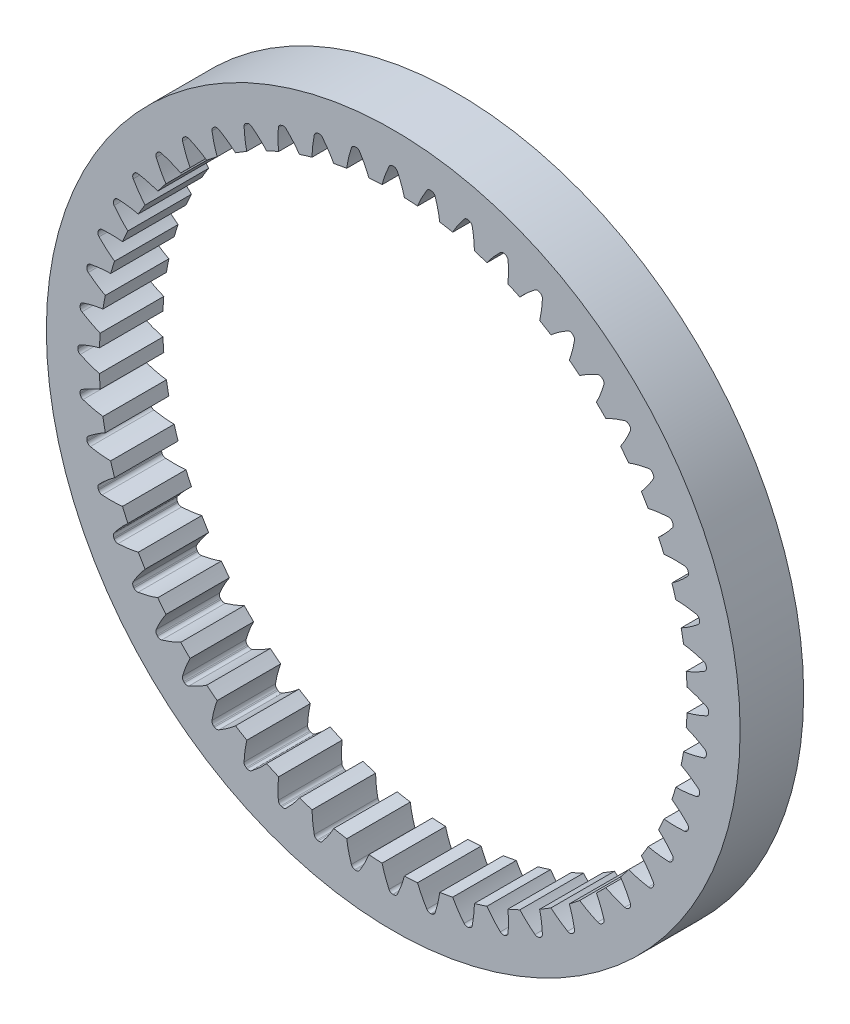
SolidWorks part; units mm, degrees
ref_plane "Front Plane" through (0, 0, 0) normal (0, 0, 1) x (1, 0, 0)
ref_plane "Top Plane" through (0, 0, 0) normal (0, 1, 0) x (1, 0, 0)
ref_plane "Right Plane" through (0, 0, 0) normal (1, 0, 0) x (0, 0, -1)
ref_axis "Axis1" through (0, 0, 2.8875) along (0, 0, -1)
sketch "Sketch3" plane through (0, 0, 0) normal (0, 0, 1) x (1, 0, 0)
  circle A0 centre (0, 0) radius 15.015
  circle A1 centre (0, 0) radius 12.725
  dimension "D1" = 30.03
  dimension "D2" = 25.45
extrude "Boss-Extrude2" add sketch "Sketch3" along normal blind 2.75
sketch "Sketch1" plane through (0, 0, 0) normal (0, 0, 1) x (1, 0, 0)
  line L8 (13.5488, 0.1808) -> (13.5488, -0.1808) construction
  line L10 (12.7158, 0.4827) -> (12.7158, -0.4827)
  line L11 (13.65, 0.0227) -> (13.65, -0.0227)
  circle A0 centre (0, 0) radius 12.725 construction
  circle A4 centre (0, 0) radius 13.65 construction
  arc A5 (13.5488, 0.1808) -> (13.65, 0.0227) centre (13.4753, 0.0224) cw
  arc A6 (13.5488, -0.1808) -> (13.65, -0.0227) centre (13.4753, -0.0224) ccw
  spline S0 degree 4 poles (12.6523, 0.498) (12.6569, 0.4969) (12.6657, 0.4949) (12.6776, 0.4921) (12.7085, 0.4845) (12.7233, 0.4808) (12.761, 0.4711) (12.7837, 0.465) (12.8146, 0.4565) (12.8404, 0.4491) (12.8693, 0.4407) (12.8962, 0.4326) (12.9242, 0.4241) (12.9514, 0.4155) (12.9791, 0.4066) (13.0063, 0.3976) (13.0338, 0.3884) (13.0661, 0.3773) (13.1057, 0.3633) (13.1509, 0.347) (13.2043, 0.3268) (13.2565, 0.3066) (13.3125, 0.284) (13.3618, 0.2638) (13.4214, 0.238) (13.4633, 0.2199) (13.5299, 0.1896) (13.5582, 0.1765) (13.601, 0.1564) (13.619, 0.1477) (13.6288, 0.143) knots 0 0 0 0 0 0.015716 0.031433 0.062363 0.090067 0.117772 0.145476 0.173181 0.200885 0.22859 0.256294 0.283999 0.311703 0.339408 0.367112 0.394817 0.422521 0.471488 0.526897 0.582306 0.637715 0.693124 0.748533 0.803942 0.859351 0.91476 0.95738 1 1 1 1 1 construction
  spline S1 degree 4 poles (12.7158, 0.4827) (12.7218, 0.4812) (12.7335, 0.4782) (12.761, 0.4711) (12.7837, 0.465) (12.8146, 0.4565) (12.8404, 0.4491) (12.8693, 0.4407) (12.8962, 0.4326) (12.9242, 0.4241) (12.9514, 0.4155) (12.9791, 0.4066) (13.0063, 0.3976) (13.0338, 0.3884) (13.0661, 0.3773) (13.1057, 0.3633) (13.1509, 0.347) (13.2043, 0.3268) (13.2565, 0.3066) (13.3125, 0.284) (13.3618, 0.2638) (13.4214, 0.238) (13.4633, 0.2199) (13.5163, 0.1958) (13.5376, 0.186) (13.5488, 0.1808) knots 0.062363 0.062363 0.062363 0.062363 0.062363 0.090067 0.117772 0.145476 0.173181 0.200885 0.22859 0.256294 0.283999 0.311703 0.339408 0.367112 0.394817 0.422521 0.471488 0.526897 0.582306 0.637715 0.693124 0.748533 0.803942 0.859351 0.91476 0.91476 0.91476 0.91476 0.91476
  spline S2 degree 4 poles (12.6523, -0.498) (12.6569, -0.4969) (12.6657, -0.4949) (12.6776, -0.4921) (12.7085, -0.4845) (12.7233, -0.4808) (12.761, -0.4711) (12.7837, -0.465) (12.8146, -0.4565) (12.8404, -0.4491) (12.8693, -0.4407) (12.8962, -0.4326) (12.9242, -0.4241) (12.9514, -0.4155) (12.9791, -0.4066) (13.0063, -0.3976) (13.0338, -0.3884) (13.0661, -0.3773) (13.1057, -0.3633) (13.1509, -0.347) (13.2043, -0.3268) (13.2565, -0.3066) (13.3125, -0.284) (13.3618, -0.2638) (13.4214, -0.238) (13.4633, -0.2199) (13.5299, -0.1896) (13.5582, -0.1765) (13.601, -0.1564) (13.619, -0.1477) (13.6288, -0.143) knots 0 0 0 0 0 0.015716 0.031433 0.062363 0.090067 0.117772 0.145476 0.173181 0.200885 0.22859 0.256294 0.283999 0.311703 0.339408 0.367112 0.394817 0.422521 0.471488 0.526897 0.582306 0.637715 0.693124 0.748533 0.803942 0.859351 0.91476 0.95738 1 1 1 1 1 construction
  spline S3 degree 4 poles (12.7158, -0.4827) (12.7218, -0.4812) (12.7335, -0.4782) (12.761, -0.4711) (12.7837, -0.465) (12.8146, -0.4565) (12.8404, -0.4491) (12.8693, -0.4407) (12.8962, -0.4326) (12.9242, -0.4241) (12.9514, -0.4155) (12.9791, -0.4066) (13.0063, -0.3976) (13.0338, -0.3884) (13.0661, -0.3773) (13.1057, -0.3633) (13.1509, -0.347) (13.2043, -0.3268) (13.2565, -0.3066) (13.3125, -0.284) (13.3618, -0.2638) (13.4214, -0.238) (13.4633, -0.2199) (13.5163, -0.1958) (13.5376, -0.186) (13.5488, -0.1808) knots 0.062363 0.062363 0.062363 0.062363 0.062363 0.090067 0.117772 0.145476 0.173181 0.200885 0.22859 0.256294 0.283999 0.311703 0.339408 0.367112 0.394817 0.422521 0.471488 0.526897 0.582306 0.637715 0.693124 0.748533 0.803942 0.859351 0.91476 0.91476 0.91476 0.91476 0.91476
  dimension "D1" = 25.45
  dimension "D3" = 27.3
extrude "Cut-Extrude2" cut sketch "Sketch1" along normal through all
pattern_circular "CirPattern1" count 52 over 360 about axis through (0, 0, 2.8875) along (0, 0, -1) of "Cut-Extrude2"
sketch "Sketch4" plane through (0, 0, 2.75) normal (0, 0, 1) x (1, 0, 0)
  circle A0 centre (0, 0) radius 17
  circle A1 centre (0, 0) radius 15.015
  circle A2 centre (0, 0) radius 15.015 construction
  dimension "D1" = 34
extrude "width-match" [suppressed] add sketch "Sketch4" against normal up to surface (2.75 mm away)
sketch "Sketch5" plane through (0, 0, 0) normal (0, 0, 1) x (1, 0, 0)
  line L0 (1.8709, 0) -> (-9.8171, 0) construction
  line L1 (18.2, 1.2) -> (18.2, 0) construction
  circle A0 centre (17, 0) radius 1 construction
  arc A1 (18.2, 2.2) -> (18.2, -2.2) centre (18.2, 0) ccw
  arc A2 (18.2, 0.2) -> (18.2, -0.2) centre (18.2, 0) ccw
  arc A4 (18.2, 2.2) -> (18.2, 0.2) centre (18.2, 1.2) cw
  arc A5 (18.2, -2.2) -> (18.2, -0.2) centre (18.2, -1.2) ccw
  dimension "D1" = 2.2
  dimension "D2" = 1
  dimension "D3" = 17
extrude "Cut-Extrude3" [suppressed] cut sketch "Sketch5" against normal through all both and the other way through all
pattern_circular "CirPattern2" [suppressed] count 4 over 360 about axis through (0, 0, 2.8875) along (0, 0, -1)
equation "\"S1_Module\"= 0.5\t\t'tooth per mm"
equation "\"R1_NumTeeth\"= 52"
equation "\"P1_teeth\"= 10"
equation "\"R2_teeth\"= 51"
equation "\"S1_PressureAngle\"= 20'deg. leave unitless"
equation "\"sun_teeth\"= \"R1_NumTeeth\" - 2 * \"P1_teeth\""
equation "\"S2_Module\"= 0.5121951219512195\t\t\t'stage two gear modules CAN be different from stage 1; this makes things a lot more complicated though so try and avoid it if you can"
equation "\"S2_PressureAngle\"= \"S1_PressureAngle\"'stage two pressure angle can be different, but for simplicity keep it the same"
equation "\"S1_carrier_radius\"= \"P1_teeth\" * \"S1_Module\" / 2  + \"sun_teeth\" * \"S1_Module\" / 2"
equation "\"P2_teeth\" = 10"
equation "\"Ring_profile_shift\" = 0.05"
equation "\"Planet_profile_shift\" = -0.05"
equation "\"Planet_broachcutter_offset\" = -0.0"
equation "\"Ring_broachcutter_offset\" = 0.0"
equation "\"Nteeth\"= \"R1_NumTeeth\""
equation "\"module\"= \"S1_Module\""
equation "\"pressure_angle\"= \"S1_PressureAngle\" * pi / 180"
equation "\"x_shift\"= \"Ring_profile_shift\""
equation "\"r_p\"= \"module\" * \"Nteeth\" / 2'pitch circle radius"
equation "\"r_b\"= \"r_p\" * cos ( \"pressure_angle\" )'base circle radius"
equation "\"r_f\"= \"r_p\" + \"module\" * ( 1.25 + \"x_shift\" )"
equation "\"head\"= - 0.4 'Default. A clearance parameter applied to the addendum in internal gears. Removes material for clearance"
equation "\"r_a\"= \"r_p\" - \"module\" * ( 1 - \"x_shift\" + \"head\" ) 'addendum"
equation "\"ttoaddendum\"= sqr ( ( \"r_a\" / \"r_b\" ) * ( \"r_a\" / \"r_b\" ) - 1 )"
equation "\"tmax\"= sqr ( ( ( \"r_f\" - 0.1 ) / \"r_b\" ) ^ 2 - 1 )"
equation "\"toothoffset\"= pi / \"Nteeth\"'Kludge. If odd number of teeth, remove the *0. If even, add a *0. Its to clock the midplane to the void between teeth for alignment in planetary stacks"
equation "\"t_p\"= sqr ( ( \"r_p\" / \"r_b\" ) ^ 2 - 1 )'t at pitch circle"
equation "\"x_p\"= \"r_b\" * ( cos ( \"t_p\" ) + \"t_p\" * sin ( \"t_p\" ) )"
equation "\"y_p\"= \"r_b\" * ( sin ( \"t_p\" ) - \"t_p\" * cos ( \"t_p\" ) )"
equation "\"theta_p\"= atn ( \"y_p\" / \"x_p\" )"
equation "\"des_ang\"= ( pi / 2 - 2 * \"x_shift\" * tan ( \"pressure_angle\" ) ) / \"Nteeth\""
equation "\"delta\"= \"des_ang\" - \"theta_p\""
equation "\"delta2\"= \"delta\" + 2 * pi * ( \"Nteeth\" - 1 ) / \"Nteeth\""
equation "\"height\"=2.75"
equation "\"involute_offset\"= \"Ring_broachcutter_offset\"'Hit CTL+q after changing this or it wont update properly"
equation "\"D1@Sketch1\"=\"r_a\"*2"
equation "\"D1@Sketch3\"=\"r_f\"*2.2"
equation "\"D2@Sketch3\"=(\"r_a\"+\"involute_offset\")*2"
equation "\"D3@Sketch1\"=\"r_f\"*2"
equation "\"D1@CirPattern1\"=\"Nteeth\""
equation "\"D1@Boss-Extrude2\"=\"height\""
